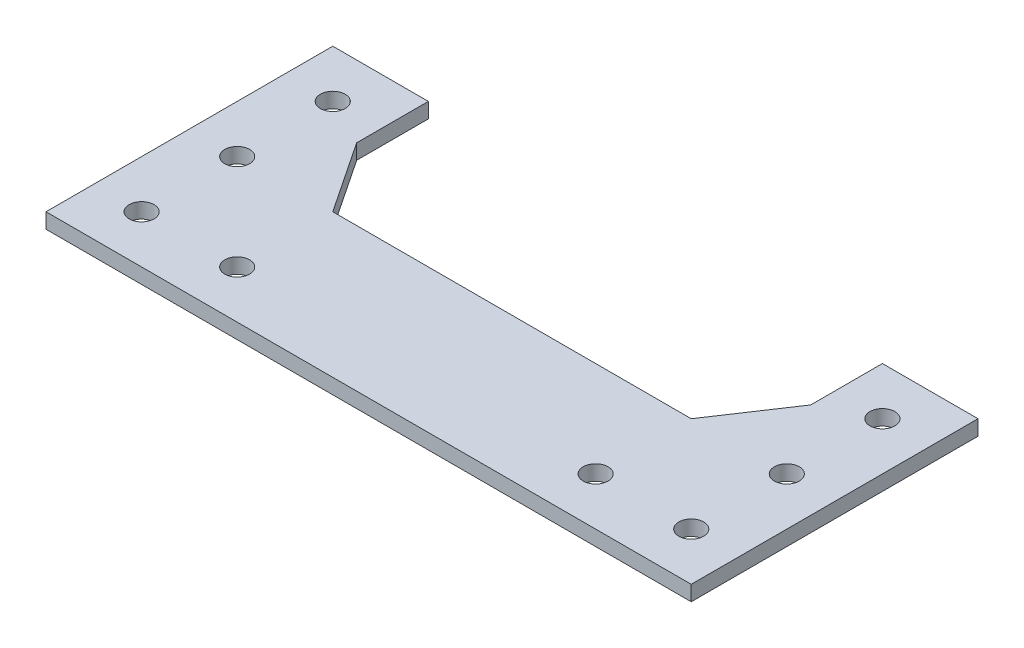
SolidWorks part; units mm, degrees
material "6061-T6 (SS)"
ref_plane "Front Plane" through (0, 0, 0) normal (0, 0, 1) x (1, 0, 0)
ref_plane "Top Plane" through (0, 0, 0) normal (0, 1, 0) x (1, 0, 0)
ref_plane "Right Plane" through (0, 0, 0) normal (1, 0, 0) x (0, 0, -1)
sketch "Sketch1" plane through (0, 0, 0) normal (0, 1, 0) x (1, 0, 0)
  line L0 (47.5, 45) -> (37.5, 30)
  line L1 (47.5, 60) -> (47.5, 45)
  line L2 (-67.5, 0) -> (-67.5, 60)
  line L3 (-67.5, 60) -> (-47.5, 60)
  line L4 (67.5, 0) -> (-67.5, 0)
  line L5 (-47.5, 60) -> (-47.5, 45)
  line L6 (67.5, 60) -> (47.5, 60)
  line L7 (-37.5, 30) -> (37.5, 30)
  line L8 (-47.5, 45) -> (-37.5, 30)
  line L9 (67.5, 0) -> (67.5, 60)
  line L10 (0, 0) -> (0, 30) construction
  line L11 (-57.5, 60) -> (-57.5, 10) construction
  line L12 (-57.5, 10) -> (0, 10) construction
  circle A0 centre (-37.5, 10) radius 2.6
  circle A1 centre (-37.5, 30) radius 2.6 [skipped]
  circle A2 centre (-37.5, 50) radius 2.6 [skipped]
  circle A4 centre (-57.5, 10) radius 2.6
  circle A5 centre (-57.5, 30) radius 2.6
  circle A6 centre (-57.5, 50) radius 2.6
  circle A9 centre (57.5, 50) radius 2.6
  circle A10 centre (57.5, 30) radius 2.6
  circle A11 centre (57.5, 10) radius 2.6
  circle A12 centre (37.5, 10) radius 2.6
  dimension "D6" = 10
  dimension "D8" = 5.2
  dimension "D11" = 20
  dimension "D13" = 20
  dimension "D1" = 135
  dimension "D2" = 60
  dimension "D3" = 20
  dimension "D4" = 15
  dimension "D5" = 75
  dimension "D7" = 10
  dimension "D12" = 30
  dimension "D9" = 2
  dimension "D10" = 3
extrude "Boss-Extrude1" add sketch "Sketch1" along normal blind 3.175
